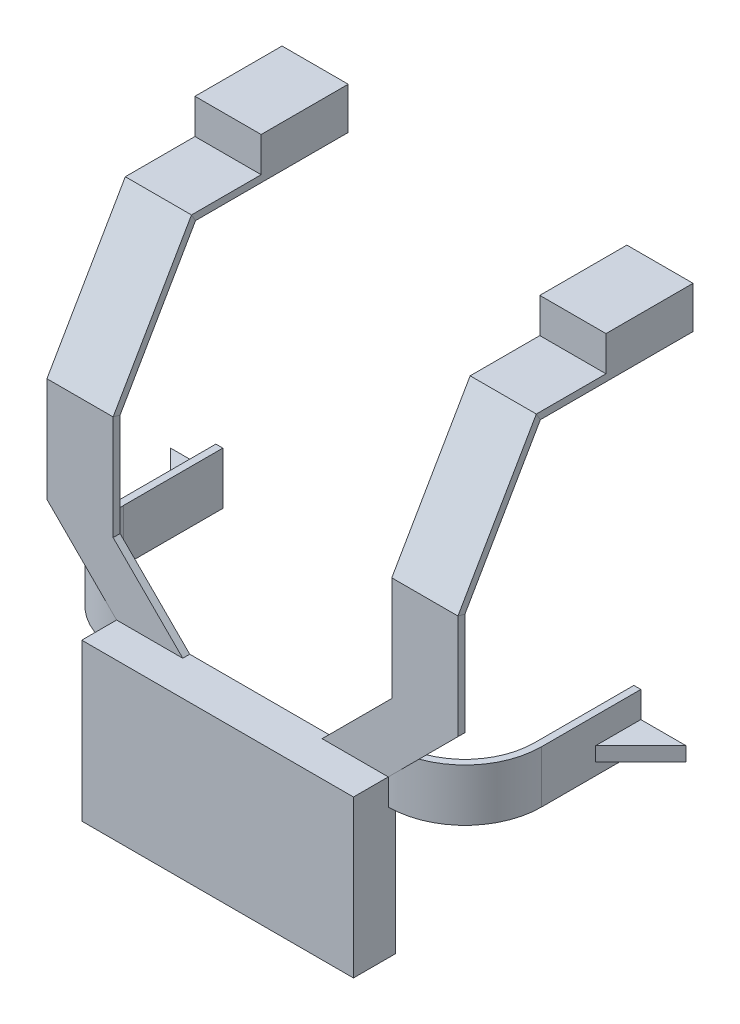
SolidWorks part; units mm, degrees
ref_plane "Front" through (0, 0, 0) normal (0, 0, 1) x (1, 0, 0)
ref_plane "Top" through (0, 0, 0) normal (0, 1, 0) x (1, 0, 0)
ref_plane "Right" through (0, 0, 0) normal (1, 0, 0) x (0, 0, -1)
sketch "草图1" plane through (0, 0, 0) normal (0, 0, 1) x (1, 0, 0)
  line L1 (0, 0) -> (0, -101.6526) construction
  line L2 (-40, 0) -> (40, 0)
  line L4 (-78, 0) -> (-78, 50)
  line L5 (-40, 50) -> (40, 50)
  line L6 (78, 0) -> (78, 50)
  line L8 (-78, 0) -> (-78, -160)
  line L9 (-78, -160) -> (-40, -160)
  line L10 (-40, 0) -> (-40, -160)
  line L12 (78, 0) -> (78, -160)
  line L13 (78, -160) -> (40, -160)
  line L14 (40, 0) -> (40, -160)
  line L15 (-143.4043, 90) -> (126.5484, 90) construction
  line L16 (-78, 50) -> (-118, 90)
  line L17 (-118, 90) -> (-80, 90)
  line L18 (-80, 90) -> (-40, 50)
  line L19 (78, 50) -> (118, 90)
  line L20 (118, 90) -> (80, 90)
  line L21 (80, 90) -> (40, 50)
  dimension "D1" = 156
  dimension "D2" = 78
  dimension "D3" = 50
  dimension "D4" = 160
  dimension "D5" = 38
  dimension "D6" = 38
  dimension "D7" = 40
  dimension "D8" = 38
  dimension "D9" = 38
extrude "凸台-拉伸1" add sketch "草图1" along normal blind 4
sketch "草图11" plane through (0, 0, 4) normal (0, 0, 1) x (1, 0, 0)
  line L0 (78, -160) -> (78, 50) construction
  line L1 (-78, 50) -> (78, 50)
  line L2 (-78, 50) -> (-78, -40)
  line L3 (-78, -40) -> (78, -40)
  line L4 (78, 50) -> (78, -40)
  dimension "D1" = 90
extrude "凸台-拉伸2" add sketch "草图11" along normal blind 20
sketch "草图12" plane through (0, 90, 0) normal (0, 1, 0) x (1, 0, 0)
  line L1 (-118, 0) -> (-80, 0)
  line L2 (-118, 0) -> (-118, -4)
  line L3 (-118, -4) -> (-80, -4)
  line L4 (-80, 0) -> (-80, -4)
  line L5 (118, 0) -> (80, 0)
  line L6 (118, 0) -> (118, -4)
  line L7 (118, -4) -> (80, -4)
  line L8 (80, 0) -> (80, -4)
sketch "草图13" plane through (78, 0, 0) normal (1, 0, 0) x (0, 0, -1)
  line L0 (-4, 90) -> (-4, 150)
  line L3 (-4, 150) -> (41, 227.9423)
  line L4 (41, 227.9423) -> (131, 227.9423)
  dimension "D1" = 60
  dimension "D2" = 150
  dimension "D3" = 90
  dimension "D5" = 90
sweep "扫描1" add profiles "草图12" path "草图13"
sketch "草图14" plane through (0, 227.9423, 0) normal (0, 1, 0) x (1, 0, 0)
  line L0 (-80, 41) -> (-80, 131) construction
  line L1 (-118, 131) -> (-80, 131)
  line L2 (-118, 131) -> (-118, 81)
  line L3 (-118, 81) -> (-80, 81)
  line L4 (-80, 131) -> (-80, 81)
  line L5 (80, 41) -> (80, 131) construction
  line L6 (118, 131) -> (80, 131)
  line L7 (118, 131) -> (118, 81)
  line L8 (118, 81) -> (80, 81)
  line L9 (80, 131) -> (80, 81)
  dimension "D1" = 50
  dimension "D2" = 50
extrude "凸台-拉伸3" add sketch "草图14" along normal blind 20
sketch "草图16" plane through (0, 0, 0) normal (0, 0, -1) x (-1, 0, 0)
  line L0 (15.8437, -40) -> (-148.9308, -40) construction
  line L1 (40, -40) -> (-40, -40) construction
  line L3 (-110.3778, -40) -> (127.8058, -40)
  line L4 (-110.3778, -40) -> (-110.3778, -172.2953)
  line L5 (-110.3778, -172.2953) -> (127.8058, -172.2953)
  line L6 (127.8058, -40) -> (127.8058, -172.2953)
extrude "切除-拉伸1" cut sketch "草图16" against normal blind 10
sketch "草图17" plane through (0, -40, 0) normal (0, -1, 0) x (1, 0, 0)
  line L0 (0, 0) -> (0, 25.1207) construction
  line L1 (-20, 0) -> (20, 0)
  line L2 (-20, 0) -> (-20, 20)
  line L3 (-20, 20) -> (20, 20)
  line L4 (20, 0) -> (20, 20)
  dimension "D1" = 40
  dimension "D2" = 20
  dimension "D3" = 20
extrude "凸台-拉伸4" add sketch "草图17" along normal blind 4
sketch "草图21" plane through (0, -44, 0) normal (0, -1, 0) x (1, 0, 0)
  line L0 (-20, 0) -> (20, 0) construction
  circle A0 centre (0, 9.5) radius 6
  dimension "D1" = 9.5
extrude "凸台-拉伸8" add sketch "草图21" along normal blind 4
sketch "草图28" plane through (0, 50, 0) normal (0, 1, 0) x (1, 0, 0)
  line L0 (-78, -4) -> (-78, 0) construction
  line L1 (-40, -4) -> (-80, -4) construction
  line L2 (-78, -24) -> (-78, -4) construction
  line L3 (-40, 0) -> (-80, 0) construction
  line L4 (-118, 97) -> (-118, -25.7453) construction
  line L7 (-78, 0) -> (-126.1781, 48.1781) construction
  line L8 (-122, 40) -> (-122, 97)
  line L9 (-122, 97) -> (-118, 97)
  line L10 (-118, 97) -> (-118, 40)
  line L11 (-78, -4) -> (-78, 0)
  line L12 (78, -4) -> (78, 102.1257) construction
  line L13 (-78, 40) -> (78, 40) construction
  line L14 (118, -4) -> (118, 41) construction
  line L15 (-118, 97) -> (169.0103, 97) construction
  line L16 (118, 40) -> (118, 97)
  line L17 (118, 81) -> (118, 131) construction
  line L18 (122, 40) -> (122, 97)
  line L19 (122, 97) -> (118, 97)
  line L20 (78, 0) -> (78, -4)
  arc A0 (-78, 0) -> (-118, 40) centre (-78, 40) cw
  arc A1 (-78, -4) -> (-122, 40) centre (-78, 40) cw
  arc A2 (78, -4) -> (122, 40) centre (78, 40) ccw
  arc A3 (78, 0) -> (118, 40) centre (78, 40) ccw
  point P12 (78, 0)
extrude "凸台-拉伸11" add sketch "草图28" along normal mid plane 30
sketch "草图29" plane through (0, 50, 0) normal (0, 1, 0) x (1, 0, 0)
  line L0 (122, 97) -> (148, 97)
  line L1 (148, 97) -> (122, 71)
  line L2 (122, 40) -> (122, 97) construction
  line L3 (122, 71) -> (122, 97)
  line L4 (-122, 97) -> (-148, 97)
  line L5 (-148, 97) -> (-122, 71)
  line L6 (-122, 97) -> (-122, 40) construction
  line L7 (-122, 71) -> (-122, 97)
extrude "凸台-拉伸12" add sketch "草图29" against normal blind 8
